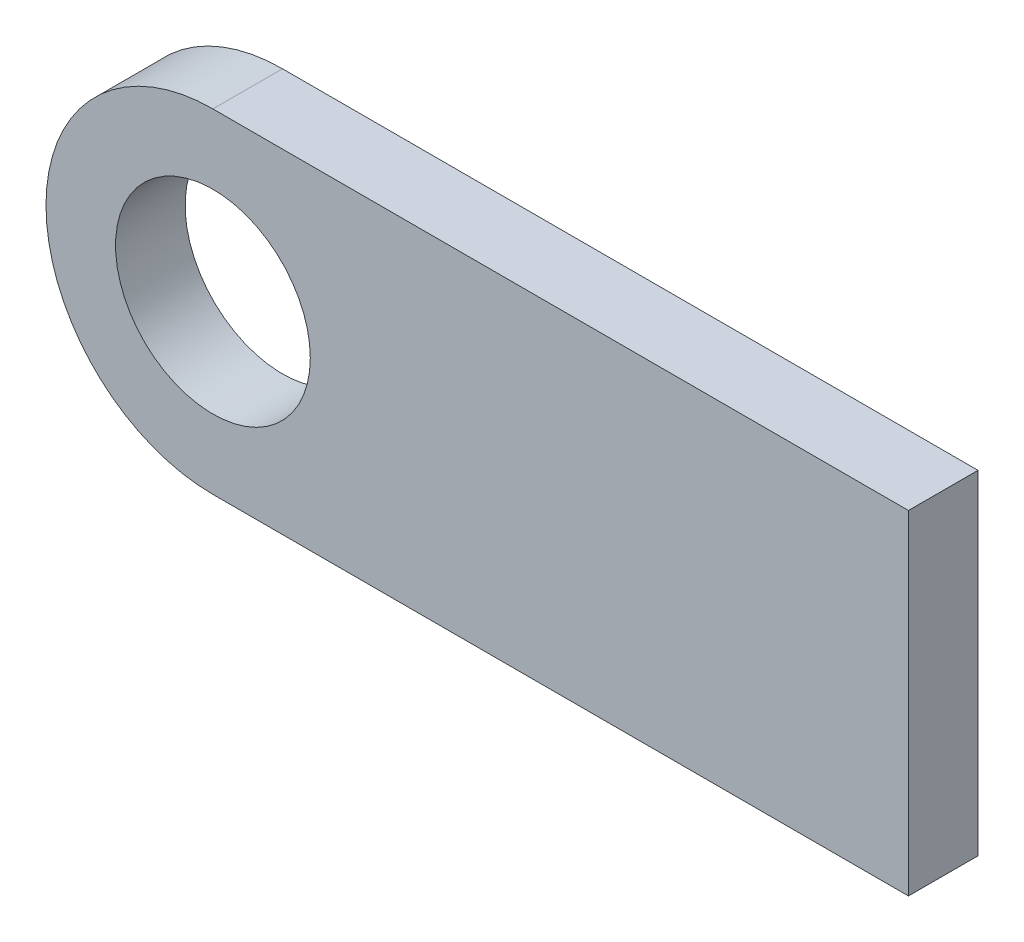
SolidWorks part; units mm, degrees
ref_plane "Płaszczyzna przednia" through (0, 0, 0) normal (0, 0, 1) x (1, 0, 0)
ref_plane "Płaszczyzna górna" through (0, 0, 0) normal (0, 1, 0) x (1, 0, 0)
ref_plane "Płaszczyzna prawa" through (0, 0, 0) normal (1, 0, 0) x (0, 0, -1)
sketch "Szkic1" plane through (0, 0, 0) normal (0, 0, 1) x (1, 0, 0)
  line L1 (0, 0) -> (50, 0)
  line L3 (0, 24) -> (50, 24)
  line L4 (50, 0) -> (50, 24)
  arc A0 (0, 24) -> (0, 0) centre (0, 12) ccw
  circle A1 centre (0, 12) radius 7
  dimension "D1" = 14
  dimension "D2" = 50
  dimension "D3" = 24
extrude "Dodanie-wyciągnięcie1" add sketch "Szkic1" along normal blind 5
